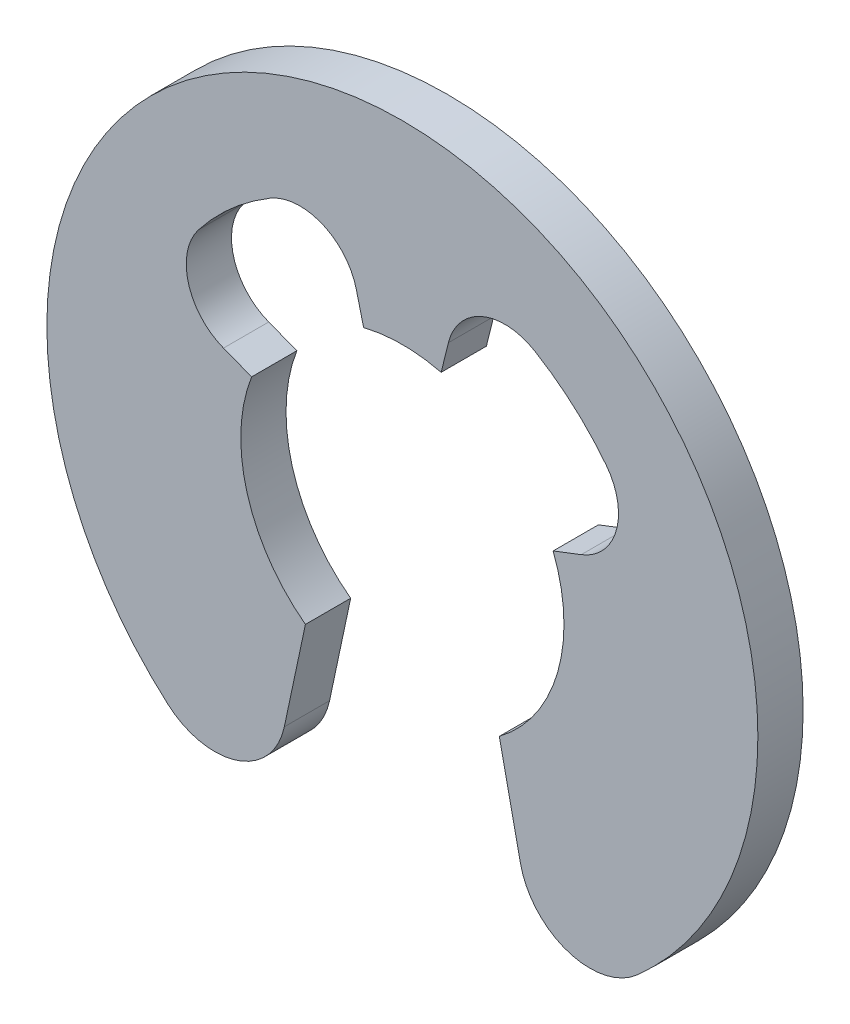
SolidWorks part; units mm, degrees
ref_plane "Plan de face" through (0, 0, 0) normal (0, 0, 1) x (1, 0, 0)
ref_plane "Plan de dessus" through (0, 0, 0) normal (0, 1, 0) x (1, 0, 0)
ref_plane "Plan de droite" through (0, 0, 0) normal (1, 0, 0) x (0, 0, -1)
sketch "Esquisse1" plane through (0, 0, 0) normal (0, 0, 1) x (1, 0, 0)
  line L0 (-1.5, -2) -> (-1.8264, -3.5357)
  line L1 (1.5, -2) -> (1.8264, -3.5357)
  line L2 (-2.3324, 0.9) -> (-2.7676, 1.0679)
  line L4 (-0.712, 2.8798) -> (-0.6, 2.4269)
  line L5 (0.6, 2.4269) -> (0.712, 2.8798)
  line L7 (2.7676, 1.0679) -> (2.3324, 0.9)
  line L8 (0, 0) -> (0, -7.5508) construction
  arc A0 (3.628, -4.1337) -> (-3.628, -4.1337) centre (0, 0) ccw
  arc A1 (1.5, -2) -> (2.3324, 0.9) centre (0, 0) ccw
  arc A2 (-2.3324, 0.9) -> (-1.5, -2) centre (0, 0) ccw
  arc A3 (0.6, 2.4269) -> (-0.6, 2.4269) centre (0, 0) ccw
  arc A5 (-2.046, 3.4371) -> (-3.153, 2.4614) centre (0, 0) ccw
  arc A6 (3.153, 2.4614) -> (2.046, 3.4371) centre (0, 0) ccw
  arc A7 (-3.153, 2.4614) -> (-2.7676, 1.0679) centre (-2.4436, 1.9076) ccw
  arc A8 (-0.712, 2.8798) -> (-2.046, 3.4371) centre (-1.5857, 2.6638) ccw
  arc A9 (2.046, 3.4371) -> (0.712, 2.8798) centre (1.5857, 2.6638) ccw
  arc A10 (2.7676, 1.0679) -> (3.153, 2.4614) centre (2.4436, 1.9076) ccw
  arc A11 (-3.628, -4.1337) -> (-1.8264, -3.5357) centre (-2.9024, -3.307) ccw
  arc A12 (3.628, -4.1337) -> (1.8264, -3.5357) centre (2.9024, -3.307) cw
  point P13 (0, 0)
  point P15 (0, 0)
  point P17 (0, 0)
  dimension "D1" = 5
  dimension "D2" = 11
  dimension "D7" = 4
  dimension "D8" = 4
  dimension "D13" = 0.9
  dimension "D14" = 0.9
  dimension "D15" = 0.9
  dimension "D16" = 0.9
  dimension "D17" = 1.1
  dimension "D18" = 1.1
  dimension "D3" = 1.5
  dimension "D4" = 1.5
  dimension "D5" = 12
  dimension "D6" = 12
  dimension "D9" = 0.6
  dimension "D10" = 0.6
  dimension "D11" = 0.9
  dimension "D12" = 0.9
extrude "Boss.-Extru.1" add sketch "Esquisse1" along normal blind 0.7
